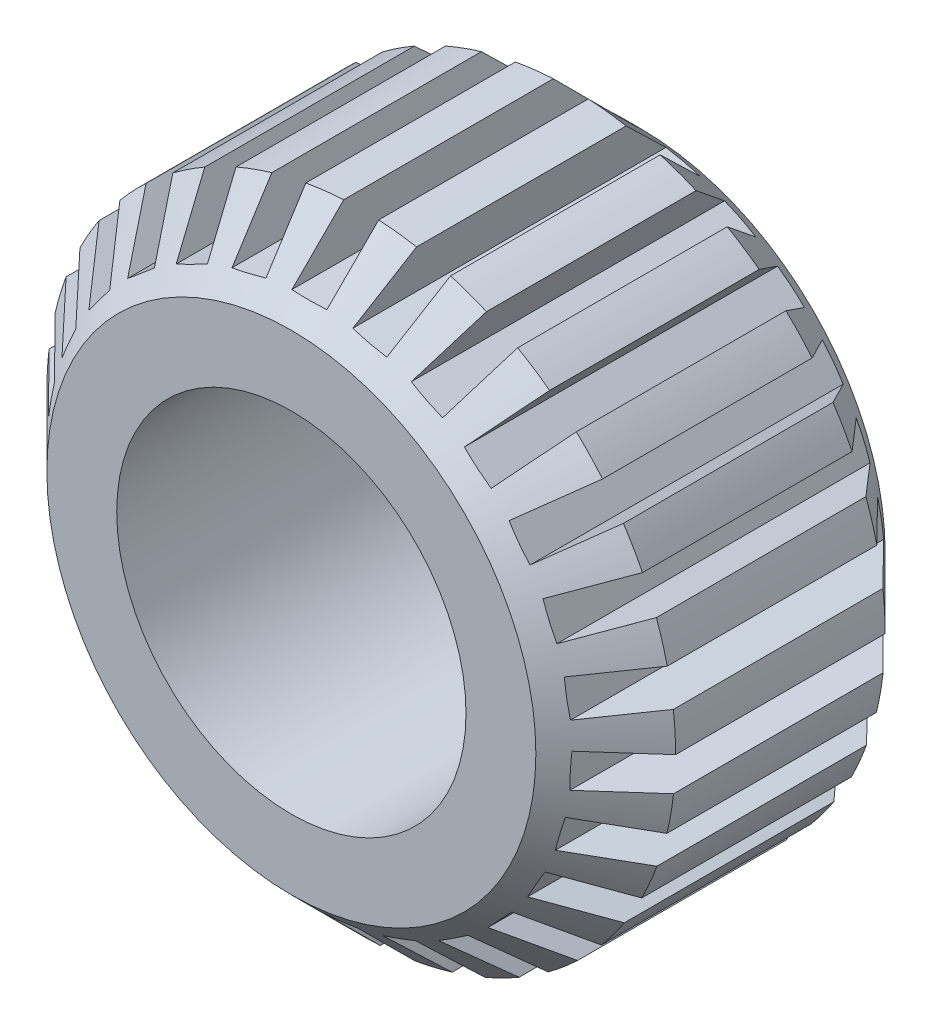
SolidWorks part; units mm, degrees
ref_plane "Front Plane" through (0, 0, 0) normal (0, 0, 1) x (1, 0, 0)
ref_plane "Top Plane" through (0, 0, 0) normal (0, 1, 0) x (1, 0, 0)
ref_plane "Right Plane" through (0, 0, 0) normal (1, 0, 0) x (0, 0, -1)
sketch "Sketch1" plane through (0, 0, 0) normal (0, 0, 1) x (1, 0, 0)
  circle A0 centre (0, 0) radius 5
  circle A1 centre (0, 0) radius 9
  circle A2 centre (0, 0) radius 1
  dimension "D1" = 10
  dimension "D2" = 4
  dimension "D3" = 4
extrude "Boss-Extrude1" add sketch "Sketch1" along normal blind 10 contours A1 A0
chamfer "Chamfer1" distance 2 angle 45 2 edges at (9, 0, 0) (9, 0, 10)
sketch "Sketch2" plane through (0, 0, 0) normal (0, 0, 1) x (1, 0, 0)
  line L0 (0, 0) -> (0, 9) construction
  line L1 (0.5, 7.5) -> (0.5, 9)
  line L2 (-0.5, 7.5) -> (-0.5, 8.9861)
  line L3 (-0.5, 7.5) -> (0.5, 7.5)
  line L5 (0.5, 0) -> (0.5, 9) construction
  line L6 (-0.5, 0) -> (-0.5, 9) construction
  circle A1 centre (0, 0) radius 9 construction
  arc A2 (0.5, 8.9861) -> (-0.5, 8.9861) centre (0, 0) ccw
  dimension "D3" = 7.5
  dimension "D1" = 0.5
  dimension "D2" = 0.5
extrude "Cut-Extrude1" cut sketch "Sketch2" along normal through all contours L1 A2 L2 L3
pattern_circular "CirPattern1" count 27 over 360 about axis through (0, 0, 0) along (0, 0, 1) of "Cut-Extrude1"
